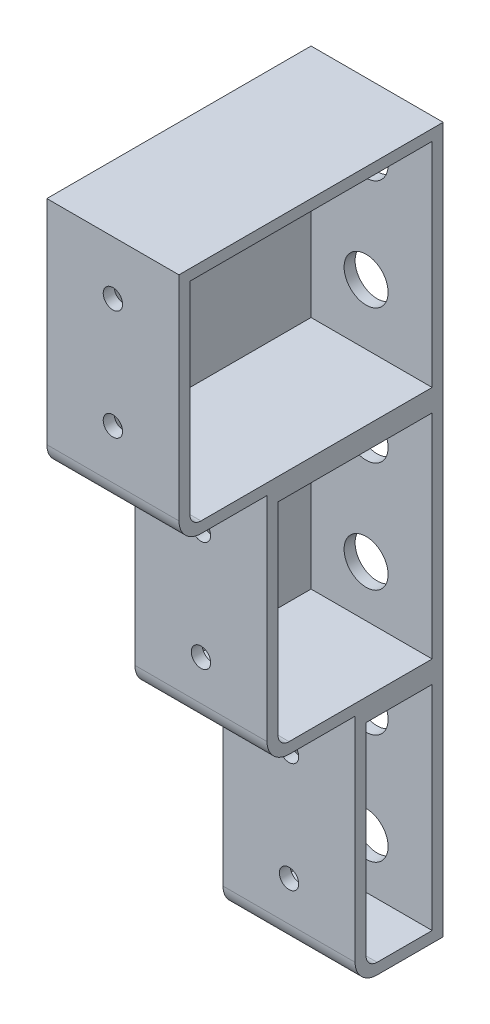
SolidWorks part; units mm, degrees
material "ABS"
ref_plane "Front Plane" through (0, 0, 0) normal (1, 0, 0) x (0, 1, 0)
ref_plane "Top Plane" through (0, 0, 0) normal (0, 0, 1) x (0, 1, 0)
ref_plane "Right Plane" through (0, 0, 0) normal (0, 1, 0) x (-1, 0, 0)
sketch "Sketch1" plane through (0, 0, 0) normal (1, 0, 0) x (0, 1, 0)
  line L1 (6.35, 25.4) -> (67.818, 25.4)
  line L2 (0, 19.05) -> (0, 0)
  line L3 (0, 0) -> (108.7438, 0)
  line L5 (74.168, 50.8) -> (135.636, 50.8)
  line L6 (67.818, 44.45) -> (67.818, 25.4)
  line L7 (108.7438, 0) -> (112.2725, 0)
  line L9 (141.986, 76.2) -> (203.454, 76.2)
  line L10 (135.636, 69.85) -> (135.636, 50.8)
  line L11 (112.2725, 0) -> (203.454, 0)
  line L12 (203.454, 76.2) -> (203.454, 0)
  arc A0 (141.986, 76.2) -> (135.636, 69.85) centre (141.986, 69.85) ccw
  arc A1 (6.35, 25.4) -> (0, 19.05) centre (6.35, 19.05) ccw
  arc A2 (74.168, 50.8) -> (67.818, 44.45) centre (74.168, 44.45) ccw
  point P19 (67.818, 32.7227)
  point P20 (135.5598, 61.0172)
  point P21 (135.5598, 64.2139)
  point P22 (204.3892, 15.5812)
  point P23 (67.818, 38.1913)
  point P24 (67.818, 34.7318)
  dimension "D7" = 6.35
  dimension "D1" = 67.818
  dimension "D2" = 67.818
  dimension "D3" = 67.818
  dimension "D4" = 25.4
  dimension "D5" = 50.8
  dimension "D6" = 76.2
extrude "Boss-Extrude1" add sketch "Sketch1" along normal mid plane 38.1
sketch "Sketch2" plane through (19.05, 0, 0) normal (1, 0, 0) x (0, 1, 0)
  line L0 (67.818, 44.45) -> (67.818, 25.4) construction
  line L1 (6.35, 22.225) -> (64.643, 22.225)
  line L2 (3.175, 19.05) -> (3.175, 3.175)
  line L3 (3.175, 3.175) -> (64.643, 3.175)
  line L4 (64.643, 22.225) -> (64.643, 3.175)
  line L5 (0, 19.05) -> (0, 0) construction
  line L6 (67.818, 25.4) -> (6.35, 25.4) construction
  line L7 (0, 0) -> (203.454, 0) construction
  line L8 (135.636, 50.8) -> (74.168, 50.8) construction
  line L9 (74.168, 47.625) -> (132.461, 47.625)
  line L10 (70.993, 44.45) -> (70.993, 3.175)
  line L11 (70.993, 3.175) -> (132.461, 3.175)
  line L12 (132.461, 47.625) -> (132.461, 3.175)
  line L13 (135.636, 69.85) -> (135.636, 50.8) construction
  line L24 (203.454, 0) -> (203.454, 76.2) construction
  line L25 (141.986, 73.025) -> (200.279, 73.025)
  line L26 (138.811, 69.85) -> (138.811, 3.175)
  line L27 (138.811, 3.175) -> (200.279, 3.175)
  line L28 (200.279, 73.025) -> (200.279, 3.175)
  line L29 (203.454, 76.2) -> (141.986, 76.2) construction
  arc A0 (141.986, 73.025) -> (138.811, 69.85) centre (141.986, 69.85) ccw
  arc A1 (74.168, 47.625) -> (70.993, 44.45) centre (74.168, 44.45) ccw
  arc A2 (6.35, 22.225) -> (3.175, 19.05) centre (6.35, 19.05) ccw
  dimension "D13" = 3.175
  dimension "D1" = 3.175
  dimension "D2" = 3.175
  dimension "D3" = 3.175
  dimension "D4" = 3.175
  dimension "D5" = 3.175
  dimension "D6" = 3.175
  dimension "D7" = 3.175
  dimension "D8" = 3.175
  dimension "D9" = 3.175
  dimension "D10" = 3.175
  dimension "D11" = 3.175
  dimension "D12" = 3.175
extrude "Cut-Extrude1" cut sketch "Sketch2" against normal blind 34.925 and the other way through all
sketch "Sketch4" plane through (0, 0, 25.4) normal (0, 0, 1) x (1, 0, 0)
  circle A0 centre (0, 17.78) radius 2.794
  circle A1 centre (0, 49.53) radius 2.794
  dimension "D1" = 5.588
  dimension "D2" = 5.588
  dimension "D3" = 17.78
  dimension "D4" = 31.75
extrude "Cut-Extrude2" cut sketch "Sketch4" against normal through all both and the other way through all
sketch "Sketch5" plane through (0, 0, 50.8) normal (0, 0, 1) x (1, 0, 0)
  circle A0 centre (0, 85.725) radius 2.794
  circle A1 centre (0, 117.475) radius 2.794
  point P7 (-12.8844, 118.2275)
  dimension "D1" = 5.588
  dimension "D2" = 5.588
  dimension "D3" = 85.725
  dimension "D4" = 31.75
extrude "Cut-Extrude3" cut sketch "Sketch5" against normal through all both and the other way through all
sketch "Sketch6" plane through (0, 0, 76.2) normal (0, 0, 1) x (1, 0, 0)
  circle A0 centre (0, 156.21) radius 2.794
  circle A1 centre (0, 187.96) radius 2.794
  point P4 (0, 0)
  dimension "D1" = 5.588
  dimension "D2" = 5.588
  dimension "D3" = 31.75
  dimension "D4" = 156.21
extrude "Cut-Extrude4" cut sketch "Sketch6" against normal through all both and the other way through all
sketch "Sketch7" plane through (0, 0, 3.175) normal (0, 0, 1) x (1, 0, 0)
  circle A0 centre (0, 17.78) radius 6.35
  circle A1 centre (0, 49.53) radius 6.35
  circle A2 centre (0, 85.725) radius 6.35
  circle A3 centre (0, 117.475) radius 6.35
  circle A4 centre (0, 156.21) radius 6.35
  circle A5 centre (0, 187.96) radius 6.35
  dimension "D1" = 12.7
  dimension "D2" = 12.7
  dimension "D3" = 12.7
  dimension "D4" = 12.7
  dimension "D5" = 12.7
  dimension "D6" = 12.7
extrude "Cut-Extrude6" cut sketch "Sketch7" against normal blind 34.925
